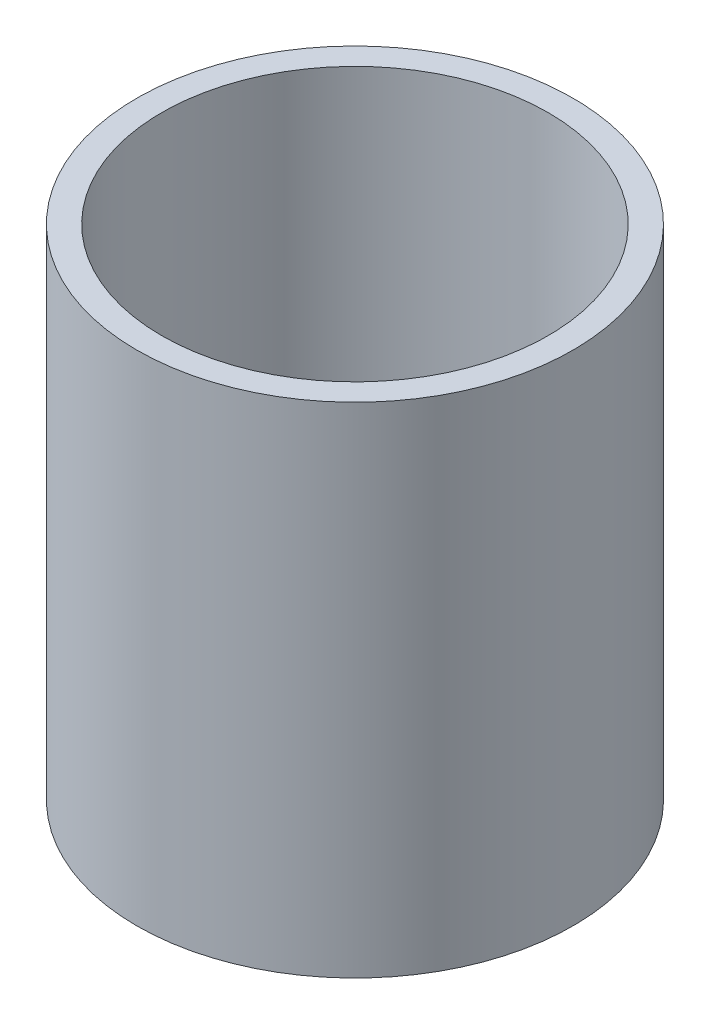
SolidWorks part; units mm, degrees
material "Epoxy, Unfilled"
ref_plane "Front Plane" through (0, 0, 0) normal (0, 0, 1) x (1, 0, 0)
ref_plane "Top Plane" through (0, 0, 0) normal (0, 1, 0) x (1, 0, 0)
ref_plane "Right Plane" through (0, 0, 0) normal (1, 0, 0) x (0, 0, -1)
sketch "Sketch1" plane through (0, 0, 0) normal (0, 1, 0) x (1, 0, 0)
  circle A0 centre (0, 0) radius 55.5625
  circle A1 centre (0, 0) radius 55.5625
  circle A2 centre (0, 0) radius 49.2125
extrude "Boss-Extrude1" add sketch "Sketch1" along normal blind 127 contours A0 A2
